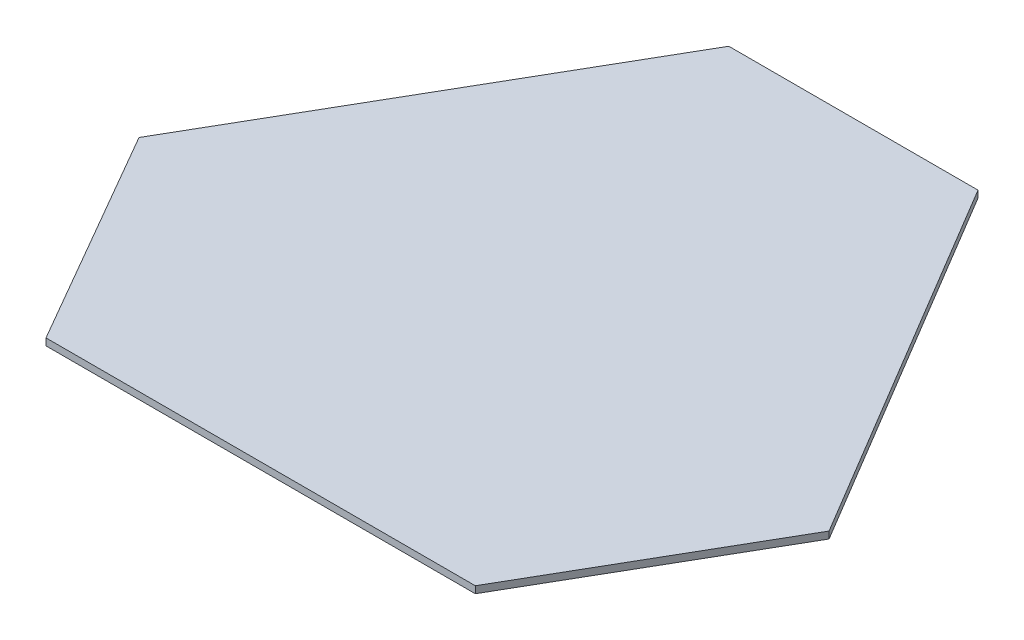
SolidWorks part; units mm, degrees
ref_plane "Front Plane" through (0, 0, 0) normal (0, 0, 1) x (1, 0, 0)
ref_plane "Top Plane" through (0, 0, 0) normal (0, 1, 0) x (1, 0, 0)
ref_plane "Right Plane" through (0, 0, 0) normal (1, 0, 0) x (0, 0, -1)
sketch "Sketch1" plane through (0, 0, 0) normal (0, 1, 0) x (1, 0, 0)
  line L0 (-178.2151, -103.6882) -> (-28.2151, 156.1194)
  line L1 (23.145, 153.5755) -> (176.9528, -103.9962)
  line L2 (150, -150) -> (-150, -150)
  line L3 (-56.6817, 106.8139) -> (51.0685, 106.8139)
  line L4 (146.5197, -53.0319) -> (90.5352, -150)
  line L5 (-150.0234, -54.8588) -> (-95.0936, -150)
  line L6 (-122.5585, -102.4294) -> (-2.8066, 106.8139)
  line L7 (-2.8066, 106.8139) -> (118.5274, -101.516)
  line L8 (118.5274, -101.516) -> (-122.5585, -102.4294)
  arc A0 (23.145, 153.5755) -> (-28.2151, 156.1194) centre (-3.3827, 137.7346) ccw
  arc A1 (150, -150) -> (176.9528, -103.9962) centre (150, -119.1025) ccw
  arc A2 (-178.2151, -103.6882) -> (-150, -150) centre (-151.4571, -119.1369) ccw
  dimension "D4" = 30.8975
  dimension "D5" = 30.8975
  dimension "D6" = 30.8975
  dimension "D1" = 300
  dimension "D2" = 300
  dimension "D3" = 300
  dimension "D7" = 150
  dimension "D8" = 150
  dimension "D9" = 60
  dimension "D10" = 60
  dimension "D11" = 60
  dimension "D12" = 60
  dimension "D13" = 60
sketch "Sketch2" plane through (0, 0, 0) normal (0, 1, 0) x (1, 0, 0)
  line L0 (-56.6817, 106.8139) -> (51.0685, 106.8139) construction
  line L1 (-178.2151, -103.6882) -> (-28.2151, 156.1194) construction
  line L2 (-150.0234, -54.8588) -> (-95.0936, -150) construction
  line L3 (150, -150) -> (-150, -150) construction
  line L4 (146.5197, -53.0319) -> (90.5352, -150) construction
  line L5 (23.145, 153.5755) -> (176.9528, -103.9962) construction
  line L6 (-56.6817, 106.8139) -> (51.0685, 106.8139)
  line L7 (-150.0234, -54.8588) -> (-56.6817, 106.8139)
  line L8 (-150.0234, -54.8588) -> (-95.0936, -150)
  line L9 (90.5352, -150) -> (-95.0936, -150)
  line L10 (146.5197, -53.0319) -> (90.5352, -150)
  line L11 (51.0685, 106.8139) -> (146.5197, -53.0319)
extrude "Boss-Extrude1" add sketch "Sketch2" along normal blind 3
